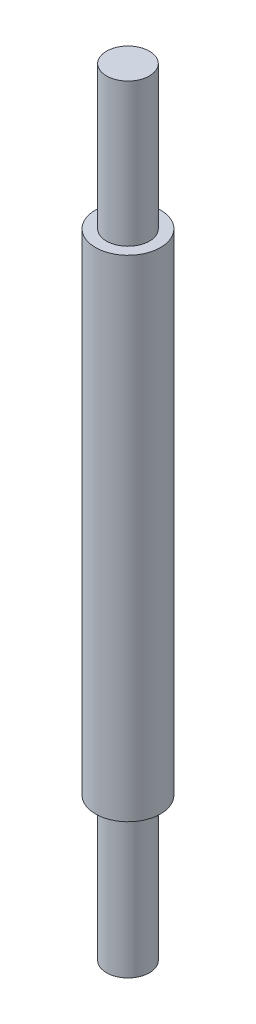
SolidWorks part; units mm, degrees
ref_plane "Front Plane" through (0, 0, 0) normal (0, 0, 1) x (1, 0, 0)
ref_plane "Top Plane" through (0, 0, 0) normal (0, 1, 0) x (1, 0, 0)
ref_plane "Right Plane" through (0, 0, 0) normal (1, 0, 0) x (0, 0, -1)
sketch "Sketch2" plane through (0, 0, 0) normal (0, 1, 0) x (1, 0, 0)
  circle A0 centre (0, 0) radius 4.0396
extrude "Boss-Extrude1" add sketch "Sketch2" along normal blind 60.96 contours A0
ref_plane "Plane2" through (0, 0, 0) normal (0, -1, 0) x (-1, 0, 0)
sketch "Sketch5" plane through (0, 0, 0) normal (0, -1, 0) x (-1, 0, 0)
  circle A0 centre (0, 0) radius 2.667
ref_plane "Plane3" through (0, 60.96, 0) normal (0, 1, 0) x (1, 0, 0)
sketch "Sketch6" plane through (0, 60.96, 0) normal (0, 1, 0) x (1, 0, 0)
  circle A0 centre (0, 0) radius 2.667
extrude "Boss-Extrude2" add sketch "Sketch6" along normal blind 17.78 contours A0
extrude "Boss-Extrude3" add sketch "Sketch5" along normal blind 17.78 contours A0
